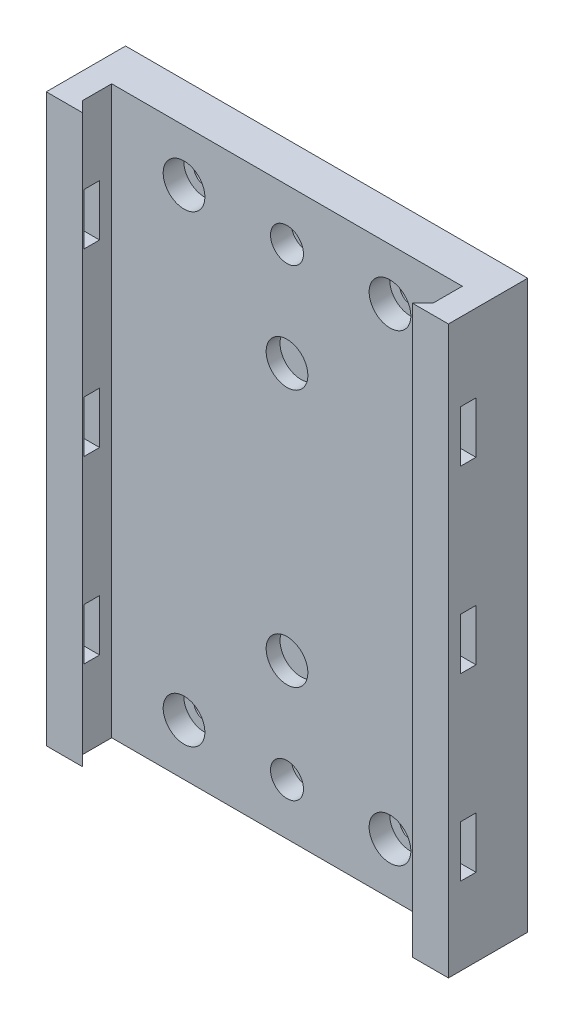
SolidWorks part; units mm, degrees
ref_plane "Front Plane" through (0, 0, 0) normal (0, 0, 1) x (1, 0, 0)
ref_plane "Top Plane" through (0, 0, 0) normal (0, 1, 0) x (1, 0, 0)
ref_plane "Right Plane" through (0, 0, 0) normal (1, 0, 0) x (0, 0, -1)
sketch "Sketch1" plane through (0, 0, 0) normal (0, 0, 1) x (1, 0, 0)
  line L6 (0, 0) -> (0, 25) construction
  line L7 (-20, 45) -> (20, 45) construction
  line L8 (-20, 45) -> (-20, -45) construction
  line L9 (-20, -45) -> (20, -45) construction
  line L10 (20, 45) -> (20, -45) construction
  line L13 (0, 25) -> (-21.6506, -12.5) construction
  line L15 (21.6506, -12.5) -> (0, 25) construction
  line L16 (0, 45) -> (0, 55) construction
  line L17 (34.05, 55) -> (-34.05, 55)
  line L18 (0, 0) -> (-10.595, 0) construction
  line L19 (34.05, -55) -> (-34.05, -55)
  line L20 (34.05, -55) -> (34.05, 55)
  line L21 (-34.05, -55) -> (-34.05, 55)
  line L22 (-21.6506, -12.5) -> (21.6506, -12.5) construction
  circle A0 centre (20, 45) radius 2.1
  circle A1 centre (-20, 45) radius 2.1
  circle A2 centre (20, -45) radius 2.1
  circle A3 centre (-20, -45) radius 2.1
  circle A4 centre (0, 0) radius 25 construction
  circle A6 centre (0, 25) radius 4.05
  circle A9 centre (0, -25) radius 4.05
  circle A10 centre (0, 45) radius 1.6
  circle A11 centre (0, -45) radius 1.6
  point P0 (0, 0)
  point P6 (0, 0)
  point P35 (0, 55)
extrude "Boss-Extrude1" add sketch "Sketch1" along normal blind 7.7
sketch "Sketch2" plane through (0, 0, 0) normal (0, 0, -1) x (-1, 0, 0)
  circle A1 centre (0, 25) radius 7.3343
  circle A3 centre (0, -25) radius 11.0737
extrude "Boss-Extrude2" add sketch "Sketch2" against normal blind 5
sketch "Sketch3" plane through (0, 0, 7.7) normal (0, 0, -1) x (-1, 0, 0)
  circle A0 centre (-20, 45) radius 4.05
  circle A1 centre (20, 45) radius 4.05
  circle A2 centre (-20, -45) radius 4.05
  circle A3 centre (20, -45) radius 4.05
  circle A4 centre (0, 45) radius 3.2
  circle A5 centre (0, -45) radius 3.2
extrude "Cut-Extrude1" cut sketch "Sketch3" along normal blind 4
sketch "Sketch4" plane through (0, 0, 7.7) normal (0, 0, 1) x (1, 0, 0)
  line L5 (-34.05, 55) -> (34.05, 55)
  line L6 (-34.05, 55) -> (-34.05, 60)
  line L7 (-34.05, 60) -> (34.05, 60)
  line L8 (34.05, 55) -> (34.05, 60)
extrude "Boss-Extrude3" add sketch "Sketch4" along normal blind 7.7 and the other way blind 7.7
sketch "Sketch7" plane through (0, -55, 0) normal (0, -1, 0) x (1, 0, 0)
  line L0 (-34.05, 15.4) -> (-32.05, 15.4)
  line L1 (-34.05, 15.4) -> (34.05, 15.4) construction
  line L4 (-34.05, 15.4) -> (-39.05, 15.4)
  line L5 (-39.05, 15.4) -> (-39.05, 0)
  line L6 (-39.05, 0) -> (-34.05, 0)
  line L8 (0, 0) -> (0, 13.1137) construction
  line L9 (-34.05, 0) -> (34.05, 0) construction
  line L11 (39.05, 0) -> (34.05, 0)
  line L12 (39.05, 15.4) -> (39.05, 0)
  line L13 (34.05, 15.4) -> (39.05, 15.4)
  line L15 (34.05, 15.4) -> (32.05, 15.4)
  line L16 (-32.05, 15.4) -> (-34.05, 13.4)
  line L17 (-34.05, 7.7) -> (-34.05, 15.4) construction
  line L18 (-34.05, 13.4) -> (-34.05, 0)
  line L19 (34.05, 13.4) -> (34.05, 0)
  line L20 (32.05, 15.4) -> (34.05, 13.4)
extrude "Boss-Extrude4" add sketch "Sketch7" against normal up to surface (115 mm away) up to face at (0, 60, 7.7)
sketch "Sketch8" plane through (0, 55, 0) normal (0, -1, 0) x (1, 0, 0)
  line L1 (46.9922, 22.7503) -> (-47.5526, 22.7503)
  line L2 (46.9922, 22.7503) -> (46.9922, -7.8306)
  line L3 (46.9922, -7.8306) -> (-47.5526, -7.8306)
  line L4 (-47.5526, 22.7503) -> (-47.5526, -7.8306)
extrude "Cut-Extrude2" cut sketch "Sketch8" against normal blind 10
sketch "Sketch9" plane through (-39.05, 0, 0) normal (-1, 0, 0) x (0, 0, 1)
  line L0 (15.4, 0) -> (7.7, 0) construction
  line L1 (15.4, 55) -> (15.4, -55) construction
  line L2 (10.05, 5) -> (13.05, 5)
  line L3 (10.05, 5) -> (10.05, -5)
  line L4 (10.05, -5) -> (13.05, -5)
  line L5 (13.05, 5) -> (13.05, -5)
  line L6 (10.05, 5) -> (13.05, -5) construction
  line L7 (10.05, -5) -> (13.05, 5) construction
  line L8 (10.05, 55) -> (10.05, 39.9) construction
  line L9 (15.4, 55) -> (0, 55) construction
  line L10 (10.05, -55) -> (10.05, -39.9) construction
  line L11 (15.4, -55) -> (0, -55) construction
  line L12 (7.7, 34.9) -> (15.4, 34.9) construction
  line L17 (10.05, 39.9) -> (13.05, 39.9)
  line L18 (10.05, 39.9) -> (10.05, 29.9)
  line L19 (7.7, -34.9) -> (15.4, -34.9) construction
  line L24 (10.05, -29.9) -> (13.05, -29.9)
  line L25 (10.05, -29.9) -> (10.05, -39.9)
  line L26 (10.05, -39.9) -> (13.05, -39.9)
  line L27 (13.05, -29.9) -> (13.05, -39.9)
  line L28 (10.05, -29.9) -> (13.05, -39.9) construction
  line L29 (10.05, -39.9) -> (13.05, -29.9) construction
  line L30 (10.05, 29.9) -> (13.05, 29.9)
  line L31 (13.05, 39.9) -> (13.05, 29.9)
  line L32 (10.05, 39.9) -> (13.05, 29.9) construction
  line L33 (10.05, 29.9) -> (13.05, 39.9) construction
  point P3 (11.55, 0)
  point P20 (11.55, 34.9)
  point P27 (11.55, -34.9)
extrude "Cut-Extrude3" cut sketch "Sketch9" against normal through all
